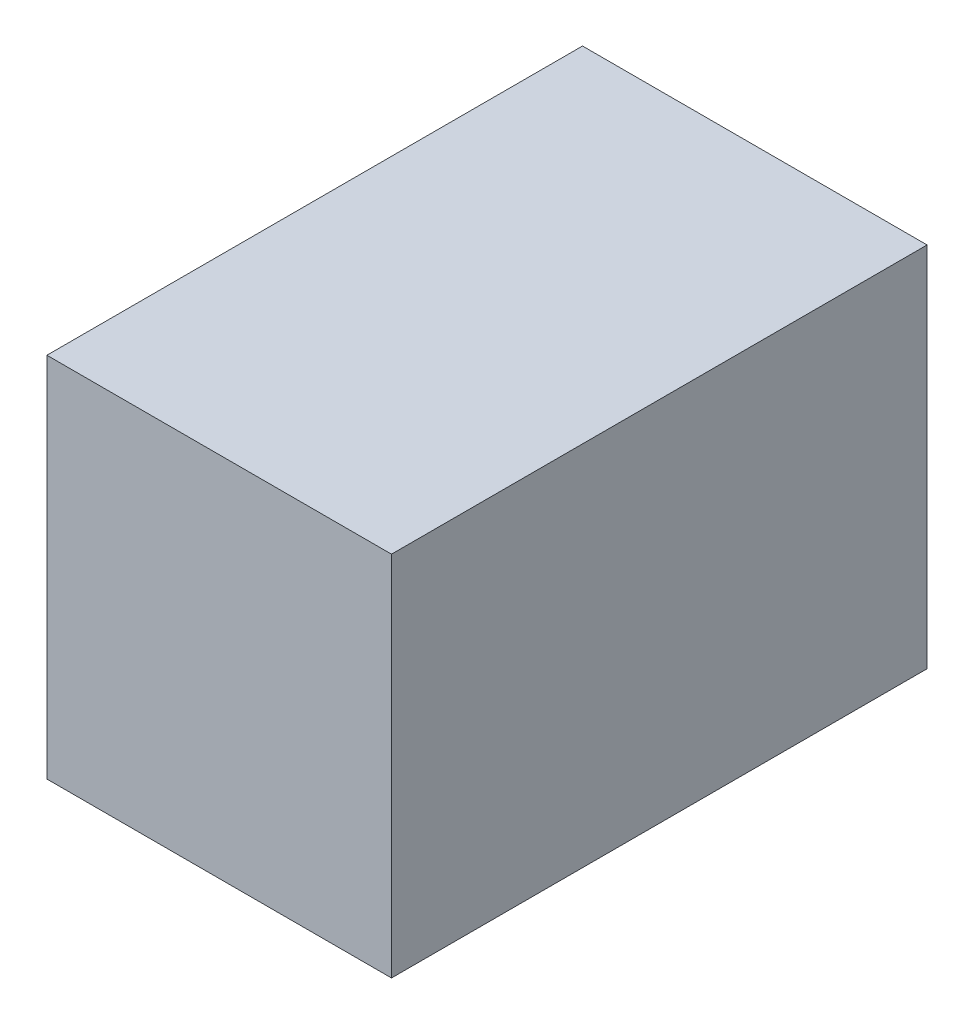
SolidWorks part; units mm, degrees
ref_plane "Front Plane" through (0, 0, 0) normal (0, 0, 1) x (1, 0, 0)
ref_plane "Top Plane" through (0, 0, 0) normal (0, 1, 0) x (1, 0, 0)
ref_plane "Right Plane" through (0, 0, 0) normal (1, 0, 0) x (0, 0, -1)
sketch "Sketch4" plane through (0, 0, 0) normal (1, 0, 0) x (0, 0, -1)
  line L1 (-15.875, 10.25) -> (15.875, 10.25)
  line L2 (-15.875, 10.25) -> (-15.875, -10.25)
  line L3 (-15.875, -10.25) -> (15.875, -10.25)
  line L4 (15.875, 10.25) -> (15.875, -10.25)
  line L5 (-15.875, 10.25) -> (15.875, -10.25) construction
  line L6 (-15.875, -10.25) -> (15.875, 10.25) construction
  point P0 (0, 0)
  dimension "D1" = 32.75
  dimension "D2" = 20.5
extrude "Boss-Extrude1" add sketch "Sketch4" along normal blind 21
shell "Shell1" thickness 2
sketch "Sketch5" plane through (0, 0, -17.875) normal (0, 0, -1) x (-1, 0, 0)
  line L0 (0, -12.25) -> (0, 12.25) construction
  line L1 (0, 10.25) -> (-12, 10.25)
  line L2 (-12, 10.25) -> (-12, -10.25)
  line L3 (-12, -10.25) -> (0, -10.25)
  line L4 (-23, 12.25) -> (0, 12.25) construction
  line L5 (-23, -12.25) -> (0, -12.25) construction
  line L6 (0, 10.25) -> (0, -10.25)
  dimension "D1" = 12
  dimension "D2" = 2
  dimension "D3" = 2
extrude "Cut-Extrude1" cut sketch "Sketch5" against normal up to surface (2 mm away) up to face at (10.5, 0, -15.875)
equation "\"terminalRad\"= 3mm"
equation "\"terminalLen\"= 10.5mm"
equation "\"threadlen\"=11"
